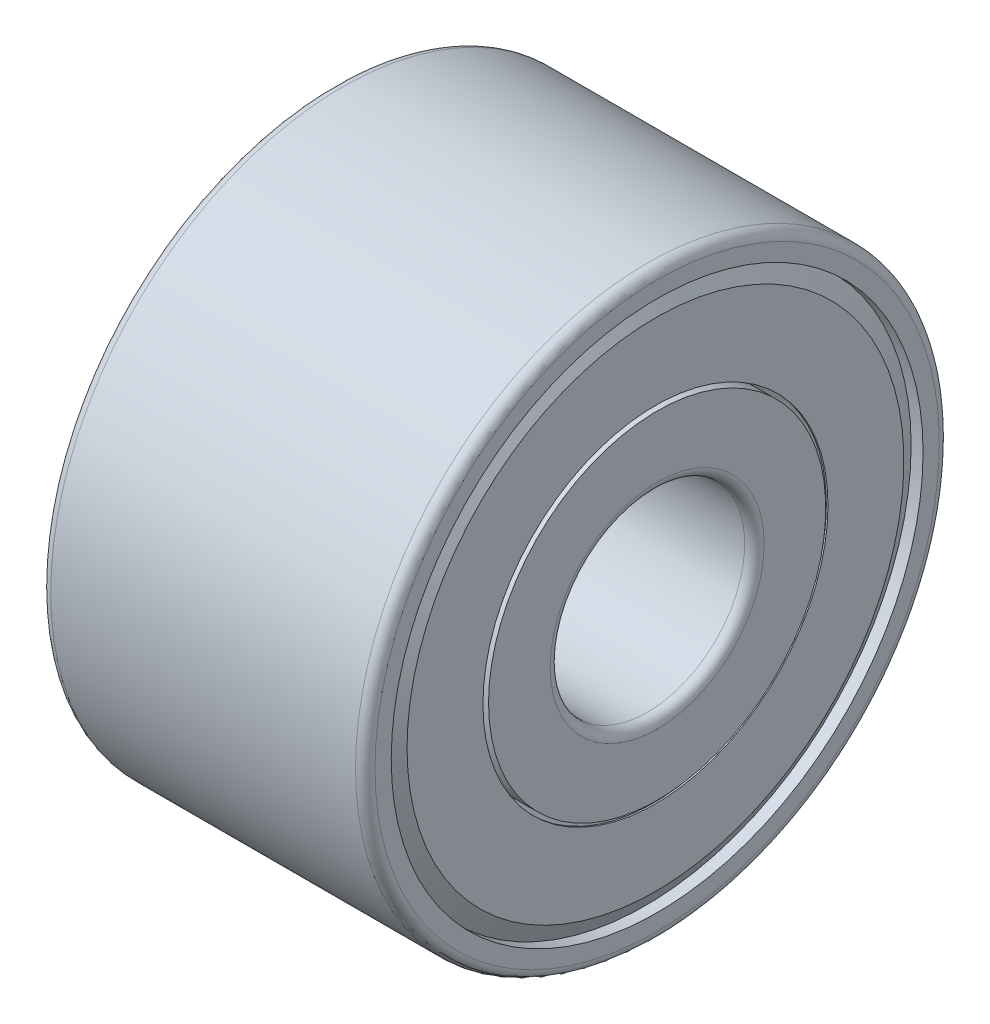
SolidWorks part; units mm, degrees
ref_plane "Plan de face" through (0, 0, 0) normal (0, 0, 1) x (1, 0, 0)
ref_plane "Plan de dessus" through (0, 0, 0) normal (0, 1, 0) x (1, 0, 0)
ref_plane "Plan de droite" through (0, 0, 0) normal (1, 0, 0) x (0, 0, -1)
ref_plane "Plan1" through (0, 0, 0) normal (0, 0, -1) x (-1, 0, 0)
sketch "Esquisse1" plane through (0, 0, 0) normal (0, 0, -1) x (-1, 0, 0)
  line L0 (-4, 2.6) -> (-4, 1.65)
  line L1 (-3.85, 1.5) -> (0.85, 1.5)
  line L2 (0.1125, 2.6) -> (1, 2.6)
  line L3 (0.6364, 3.85) -> (0.245, 3.85)
  line L4 (0.6364, 4.1) -> (0.6364, 3.85)
  line L5 (0.7382, 4.1882) -> (0.741, 4.1899)
  line L6 (0.949, 3.8231) -> (0.7382, 4.1882)
  line L7 (0.949, 2.66) -> (0.949, 3.8231)
  line L8 (0.974, 2.66) -> (0.949, 2.66)
  line L9 (0.974, 3.8298) -> (0.974, 2.66)
  line L10 (0.8158, 4.1) -> (0.974, 3.8298)
  line L11 (1, 4.1) -> (0.8158, 4.1)
  line L12 (1, 4.35) -> (1, 4.1)
  line L13 (1, 2.6) -> (1, 1.65)
  line L14 (0.85, 4.5) -> (-3.85, 4.5)
  line L15 (-4, 4.35) -> (-4, 4.1)
  line L16 (-4, 4.1) -> (-3.8158, 4.1)
  line L17 (-3.8158, 4.1) -> (-3.974, 3.8298)
  line L18 (-3.974, 3.8298) -> (-3.974, 2.66)
  line L19 (-3.974, 2.66) -> (-3.949, 2.66)
  line L20 (-3.949, 2.66) -> (-3.949, 3.8231)
  line L21 (-3.949, 3.8231) -> (-3.7382, 4.1882)
  line L22 (-3.7382, 4.1882) -> (-3.741, 4.1899)
  line L23 (-3.6364, 4.1) -> (-3.6364, 3.85)
  line L24 (-3.6364, 3.85) -> (-3.245, 3.85)
  line L25 (-3.1125, 2.6) -> (-4, 2.6)
  line L26 (-4, 0) -> (1, 0) construction
  line L27 (-1.5, 0) -> (-1.5, 4.5) construction
  arc A0 (-4, 1.65) -> (-3.85, 1.5) centre (-3.85, 1.65) ccw
  arc A1 (0.245, 3.85) -> (0.1125, 2.6) centre (-1, 3.35) cw
  arc A2 (0.741, 4.1899) -> (0.6364, 4.1) centre (0.7273, 4.1) ccw
  arc A3 (0.85, 4.5) -> (1, 4.35) centre (0.85, 4.35) cw
  arc A4 (1, 1.65) -> (0.85, 1.5) centre (0.85, 1.65) cw
  arc A6 (-3.85, 4.5) -> (-4, 4.35) centre (-3.85, 4.35) ccw
  arc A8 (-3.741, 4.1899) -> (-3.6364, 4.1) centre (-3.7273, 4.1) cw
  arc A9 (-3.245, 3.85) -> (-3.1125, 2.6) centre (-2, 3.35) ccw
  point P47 (-1.5, 1.5)
  dimension "D1" = 4.5
  dimension "D2" = 5
  dimension "D3" = 1.5
revolve "Révolution1" add sketch "Esquisse1" angle 360 about L26
